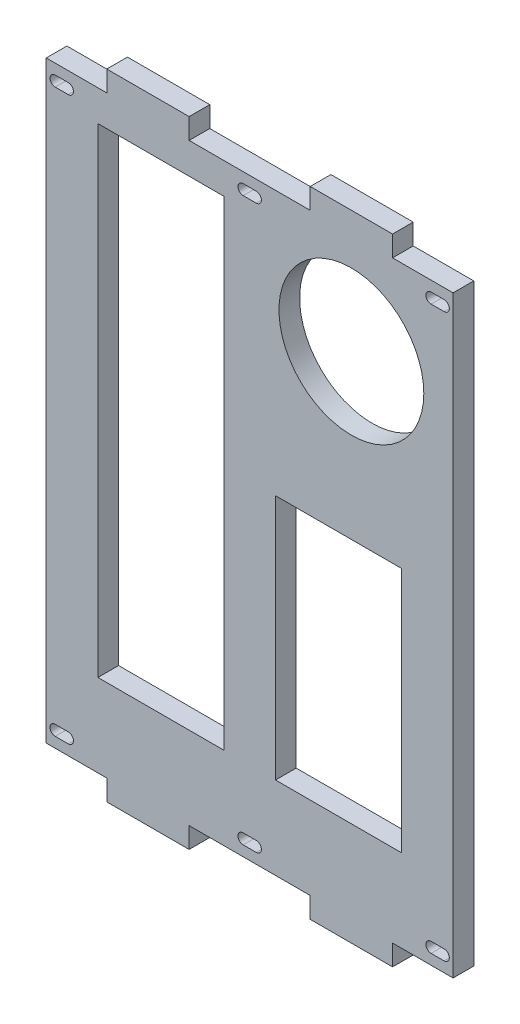
SolidWorks part; units mm, degrees
ref_plane "Alzado" through (0, 0, 0) normal (0, 0, 1) x (1, 0, 0)
ref_plane "Planta" through (0, 0, 0) normal (0, 1, 0) x (1, 0, 0)
ref_plane "Vista lateral" through (0, 0, 0) normal (1, 0, 0) x (0, 0, -1)
sketch "Croquis1" plane through (0, 0, 0) normal (0, 0, 1) x (1, 0, 0)
  line L0 (62.5, 195) -> (62.5, -195) construction
  line L1 (-125, -195) -> (125, -195)
  line L2 (-125, -195) -> (-125, 195)
  line L3 (-125, 195) -> (125, 195)
  line L4 (125, -195) -> (125, 195)
  line L5 (-125, -195) -> (125, 195) construction
  line L6 (-125, 195) -> (125, -195) construction
  line L7 (-93.25, 163.25) -> (-15.875, 163.25)
  line L8 (-93.25, 163.25) -> (-93.25, -131.5)
  line L9 (-93.25, -131.5) -> (-15.875, -131.5)
  line L10 (-15.875, 163.25) -> (-15.875, -131.5)
  line L11 (15.875, 19.8) -> (93.25, 19.8)
  line L12 (15.875, 19.8) -> (15.875, -131.5)
  line L13 (15.875, -131.5) -> (93.25, -131.5)
  line L14 (93.25, 19.8) -> (93.25, -131.5)
  line L15 (-15.875, -131.5) -> (15.875, -131.5) construction
  circle A0 centre (62.5, 119.8) radius 44.5
  point P0 (0, 0)
  point P18 (0, -131.5)
  dimension "D4" = 89
  dimension "D5" = 75.2
  dimension "D13" = 100
  dimension "D1" = 390
  dimension "D2" = 250
  dimension "D3" = 62.5
  dimension "D6" = 63.5
  dimension "D7" = 31.75
  dimension "D8" = 63.5
  dimension "D9" = 31.75
  dimension "D10" = 31.75
  dimension "D11" = 31.75
  dimension "D12" = 125
extrude "Saliente-Extruir1" add sketch "Croquis1" along normal blind 12.7 contours L3 L4 L1 L2
sketch "Croquis2" plane through (0, 0, 12.7) normal (0, 0, 1) x (1, 0, 0)
  line L0 (125, 195) -> (-125, 195) construction
  line L1 (-125, 195) -> (-87.8, 195)
  line L2 (-125, 195) -> (-125, 182.3)
  line L3 (-125, 182.3) -> (-87.8, 182.3)
  line L4 (-87.8, 195) -> (-87.8, 182.3)
  line L5 (-37.2, 195) -> (37.2, 195)
  line L6 (-37.2, 195) -> (-37.2, 182.3)
  line L7 (-37.2, 182.3) -> (37.2, 182.3)
  line L8 (37.2, 195) -> (37.2, 182.3)
  line L9 (125, -195) -> (125, 195) construction
  line L10 (87.8, 195) -> (125, 195)
  line L11 (87.8, 195) -> (87.8, 182.3)
  line L12 (87.8, 182.3) -> (125, 182.3)
  line L13 (125, 195) -> (125, 182.3)
  line L14 (-115.475, 182.3) -> (-115.475, 113.5153) construction
  line L15 (0, 182.3) -> (0, 113.5153) construction
  line L16 (115.475, 127.3) -> (115.475, 113.5153) construction
  line L17 (-125, 195) -> (-125, -195) construction
  line L22 (-119.475, 172.75) -> (-111.475, 172.75) construction
  line L23 (-119.475, 175.95) -> (-111.475, 175.95)
  line L24 (-119.475, 169.55) -> (-111.475, 169.55)
  line L25 (-4, 172.75) -> (4, 172.75) construction
  line L26 (-4, 175.95) -> (4, 175.95)
  line L27 (-4, 169.55) -> (4, 169.55)
  line L28 (111.475, 172.75) -> (119.475, 172.75) construction
  line L29 (111.475, 175.95) -> (119.475, 175.95)
  line L30 (111.475, 169.55) -> (119.475, 169.55)
  arc A0 (-119.475, 175.95) -> (-119.475, 169.55) centre (-119.475, 172.75) ccw
  arc A1 (-111.475, 169.55) -> (-111.475, 175.95) centre (-111.475, 172.75) ccw
  arc A2 (-4, 175.95) -> (-4, 169.55) centre (-4, 172.75) ccw
  arc A3 (4, 169.55) -> (4, 175.95) centre (4, 172.75) ccw
  arc A4 (111.475, 175.95) -> (111.475, 169.55) centre (111.475, 172.75) ccw
  arc A5 (119.475, 169.55) -> (119.475, 175.95) centre (119.475, 172.75) ccw
  point P27 (-115.475, 172.75)
  point P36 (0, 172.75)
  point P42 (115.475, 172.75)
  dimension "D8" = 3.2
  dimension "D10" = 8
  dimension "D11" = 3.2
  dimension "D13" = 3.2
  dimension "D1" = 12.7
  dimension "D2" = 50.6
  dimension "D3" = 50.6
  dimension "D4" = 37.2
  dimension "D5" = 37.2
  dimension "D6" = 9.525
  dimension "D7" = 9.525
  dimension "D9" = 6.35
  dimension "D12" = 8
  dimension "D14" = 8
extrude "Cortar-Extruir1" cut sketch "Croquis2" against normal through all
mirror "Simetría1" about plane through (0, 0, 0) normal (0, 1, 0) of "Cortar-Extruir1"
